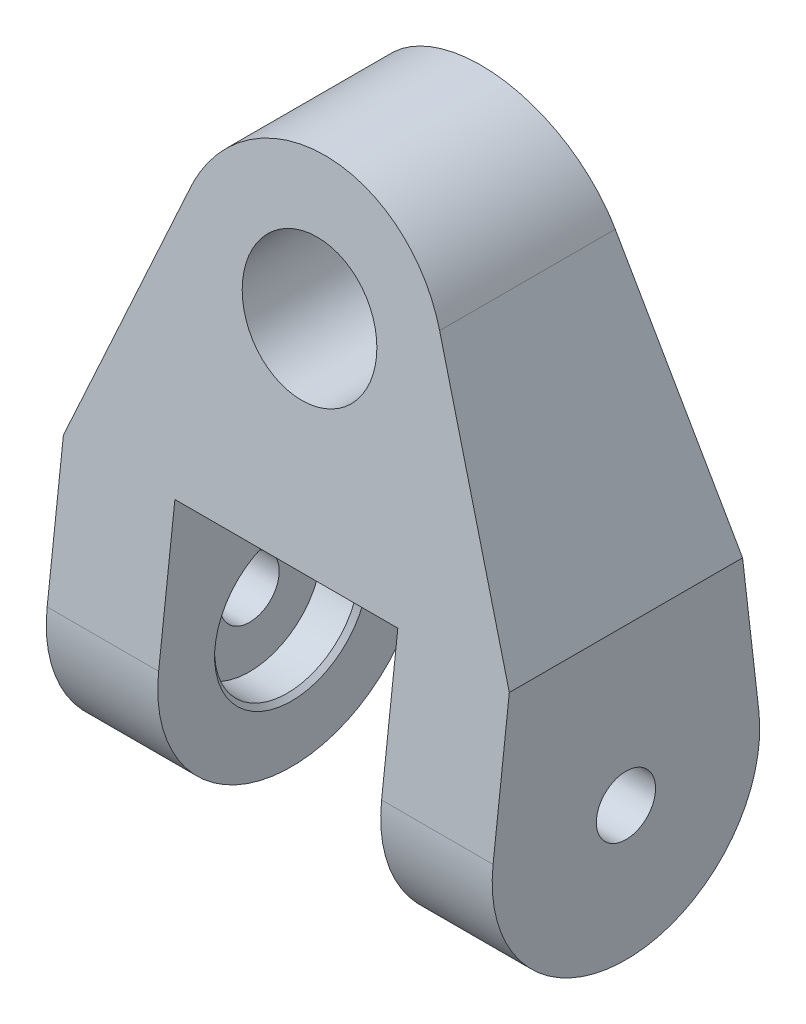
SolidWorks part; units mm, degrees
ref_plane "Front Plane" through (0, 0, 0) normal (0, 0, 1) x (1, 0, 0)
ref_plane "Top Plane" through (0, 0, 0) normal (0, 1, 0) x (1, 0, 0)
ref_plane "Right Plane" through (0, 0, 0) normal (1, 0, 0) x (0, 0, -1)
sketch "Sketch1" plane through (0, 0, 0) normal (0, 0, 1) x (1, 0, 0)
  line L0 (0, 28.575) -> (0, 0) construction
  line L1 (17.7212, 35.5652) -> (31.75, 0)
  line L2 (-17.7212, 35.5652) -> (-31.75, 0)
  line L3 (31.75, 0) -> (31.75, -41.275)
  line L4 (-31.75, 0) -> (-31.75, -41.275)
  line L5 (31.75, -41.275) -> (15.875, -41.275)
  line L6 (-31.75, -41.275) -> (-15.875, -41.275)
  line L7 (15.875, -41.275) -> (15.875, 0)
  line L8 (-15.875, -41.275) -> (-15.875, 0)
  line L9 (15.875, 0) -> (-15.875, 0)
  circle A0 centre (0, 28.575) radius 9.525
  arc A1 (17.7212, 35.5652) -> (-17.7212, 35.5652) centre (0, 28.575) ccw
  point P15 (0, 0)
  dimension "D1" = 19.05
  dimension "D2" = 19.05
  dimension "D3" = 69.85
  dimension "D4" = 41.275
  dimension "D5" = 31.75
  dimension "D6" = 15.875
  dimension "D7" = 41.275
extrude "Boss-Extrude1" add sketch "Sketch1" along normal mid plane 38.1
sketch "Sketch2" plane through (0, 0, 0) normal (1, 0, 0) x (0, 0, -1)
  line L1 (19.05, -41.275) -> (19.05, 0) construction
  line L2 (-19.05, -41.275) -> (19.05, -41.275) construction
  line L3 (0, -22.225) -> (0, 47.625) construction
  line L4 (19.05, 47.625) -> (-19.05, 47.625) construction
  line L5 (18.9243, -20.0402) -> (11.1125, 47.625)
  line L6 (-18.9243, -20.0402) -> (-11.1125, 47.625)
  line L7 (11.1125, 47.625) -> (-11.1125, 47.625)
  arc A0 (-18.9243, -20.0402) -> (18.9243, -20.0402) centre (0, -22.225) ccw
  point P1 (0, 0)
  dimension "D1" = 19.05
  dimension "D2" = 22.225
extrude "Cut-Extrude1" cut sketch "Sketch2" against normal through all and the other way through all flip side to cut
hole_wizard "CBORE for 5/16 Hex Head Bolt2" positions "Sketch5" profile "Sketch6" counterbore size "5/16" standard "ANSI Inch" end condition through all
sketch "Sketch5" plane through (-15.875, 0, 0) normal (1, 0, 0) x (0, 0, -1)
  arc A0 (-18.9243, -20.0402) -> (18.9243, -20.0402) centre (0, -22.225) ccw construction
  point P0 (0, -22.225)
sketch "Sketch6" plane through (-15.875, -22.225, 0) normal (0, 1, 0) x (0, 0, -1)
  line L0 (0, 0) -> (0, 15.875)
  line L1 (0, 15.875) -> (4.2164, 15.875)
  line L3 (4.2164, 15.875) -> (4.2164, 5.969)
  line L4 (10.3187, 5.969) -> (4.2164, 5.969)
  line L5 (10.3187, 5.969) -> (10.3187, 0.635)
  line L6 (10.3187, 0.635) -> (10.9537, 0)
  line L7 (10.9537, 0) -> (0, 0)
  line L8 (-10.3187, 0.635) -> (-10.9537, 0) construction
  line L11 (0, -6.35) -> (0, 107.95) construction
  dimension "Thru Hole Dia." = 8.4328
  dimension "Thru Hole Depth" = 15.875
  dimension "C'Bore Dia." = 20.6375
  dimension "C'Bore Depth" = 5.969
  dimension "Near C'Sink Dia." = 21.9075
  dimension "Near C'Sink Angle" = 90
mirror "Mirror1" about plane through (0, 0, 0) normal (1, 0, 0) of "CBORE for 5/16 Hex Head Bolt2"
